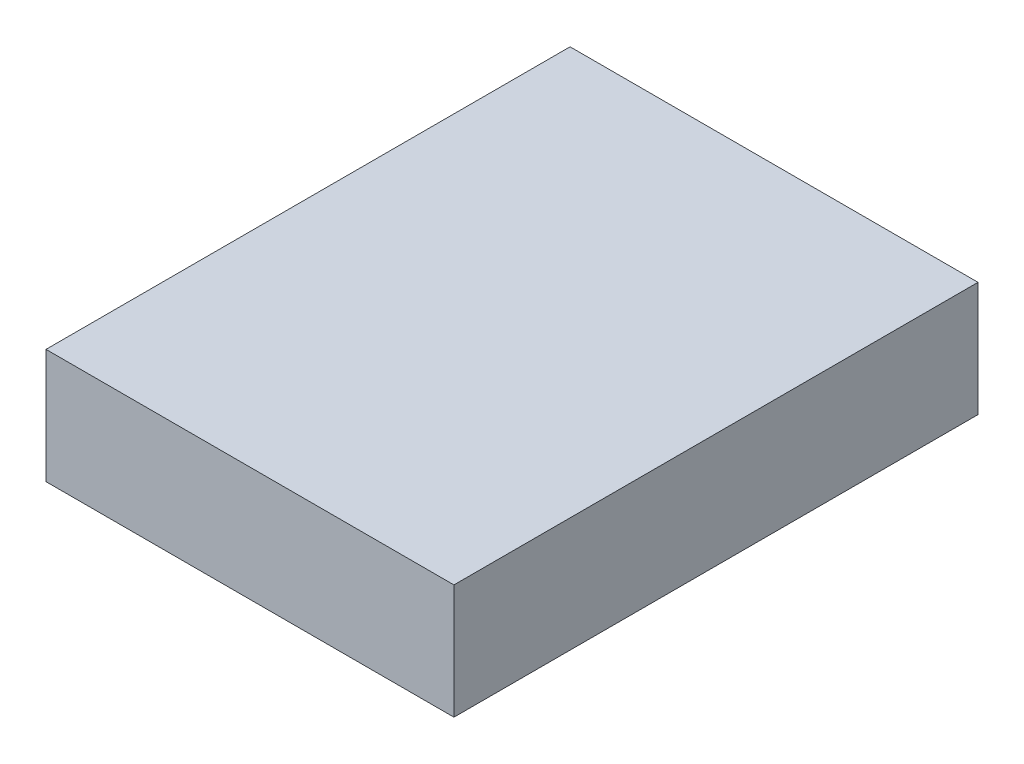
SolidWorks part; units mm, degrees
ref_plane "Front Plane" through (0, 0, 0) normal (0, 0, 1) x (1, 0, 0)
ref_plane "Top Plane" through (0, 0, 0) normal (0, 1, 0) x (1, 0, 0)
ref_plane "Right Plane" through (0, 0, 0) normal (1, 0, 0) x (0, 0, -1)
sketch "Sketch1" plane through (0, 0, 0) normal (0, 1, 0) x (1, 0, 0)
  line L0 (0, 34.3) -> (0, -34.3) construction
  line L1 (-26.7, 34.3) -> (26.7, 34.3)
  line L2 (-26.7, 34.3) -> (-26.7, -34.3)
  line L3 (-26.7, -34.3) -> (26.7, -34.3)
  line L4 (26.7, 34.3) -> (26.7, -34.3)
  line L5 (-26.7, 0) -> (26.7, 0) construction
  point P9 (0, 0)
  dimension "D1" = 68.6
  dimension "D2" = 53.4
extrude "Boss-Extrude1" add sketch "Sketch1" along normal blind 15
